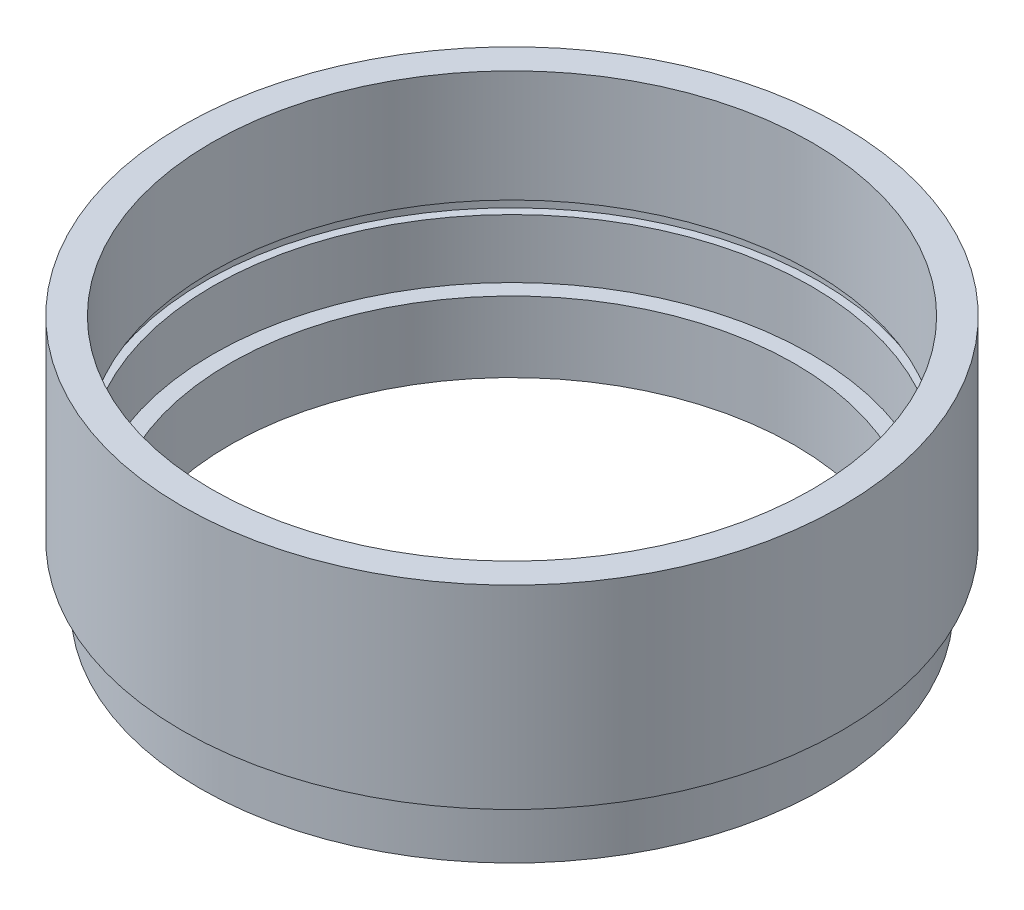
SolidWorks part; units mm, degrees
ref_plane "前视基准面" through (0, 0, 0) normal (0, 0, 1) x (1, 0, 0)
ref_plane "上视基准面" through (0, 0, 0) normal (0, 1, 0) x (1, 0, 0)
ref_plane "右视基准面" through (0, 0, 0) normal (1, 0, 0) x (0, 0, -1)
sketch "草图1" plane through (0, 0, 0) normal (0, 0, 1) x (1, 0, 0)
  line L0 (0, 0) -> (0, 21.8535) construction
  line L1 (24, 0) -> (26.5, 0)
  line L2 (26.5, 0) -> (26.5, 4)
  line L3 (26.5, 4) -> (25.5, 4)
  line L4 (25.5, 4) -> (25.5, 5)
  line L5 (25.5, 5) -> (28, 5)
  line L6 (28, 5) -> (28, 21.5)
  line L7 (28, 21.5) -> (25.5, 21.5)
  line L8 (25.5, 21.5) -> (25.5, 12)
  line L9 (25.5, 12) -> (26.1, 12)
  line L10 (26.1, 12) -> (26.1, 11)
  line L11 (26.1, 11) -> (25.4, 11)
  line L12 (25.4, 11) -> (25.4, 6)
  line L13 (25.4, 6) -> (24, 6)
  line L14 (24, 0) -> (24, 6)
  dimension "D1" = 21.5
  dimension "D2" = 28
  dimension "D3" = 25.5
  dimension "D4" = 25.4
  dimension "D5" = 1
  dimension "D6" = 5
  dimension "D7" = 24
  dimension "D8" = 26.5
  dimension "D9" = 1
  dimension "D10" = 5
  dimension "D11" = 6
  dimension "D12" = 26.1
  dimension "D13" = 25.5
revolve "旋转1" add sketch "草图1" angle 360 about L0
cosmetic thread "装饰螺纹线11"
cosmetic thread "装饰螺纹线12"
